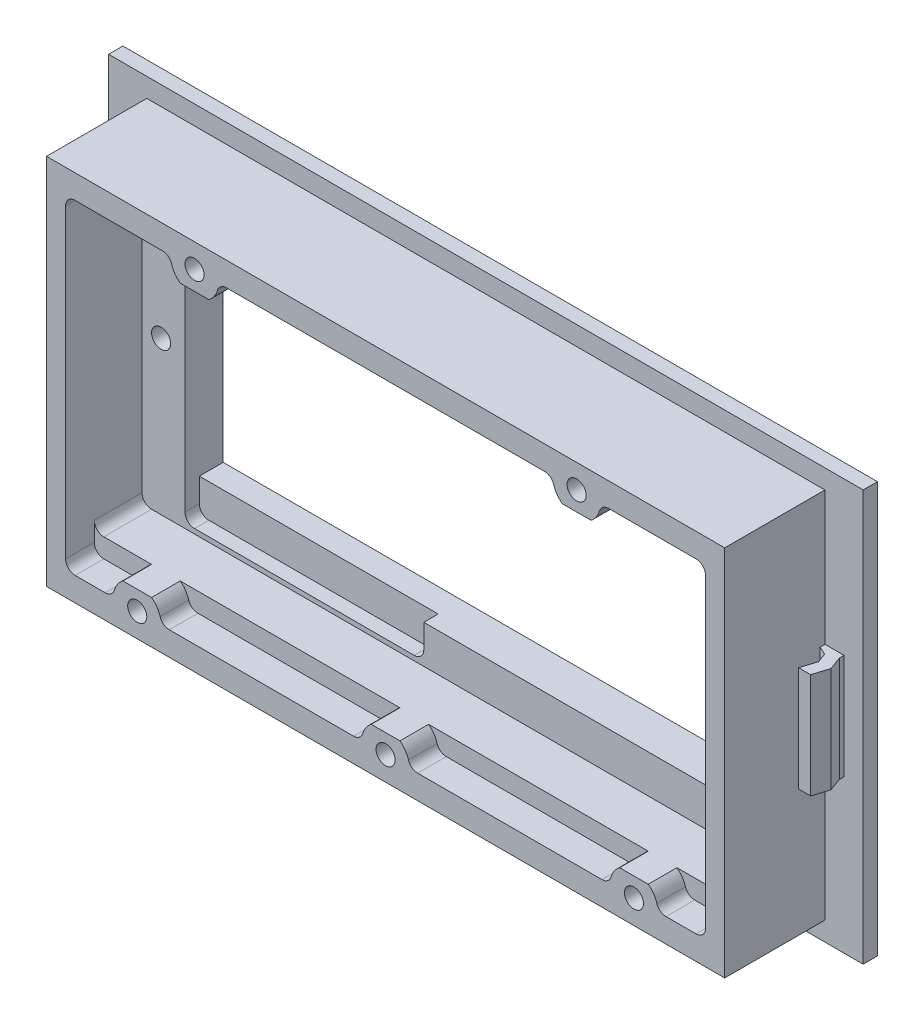
SolidWorks part; units mm, degrees
ref_plane "Спереди" through (0, 0, 0) normal (0, 0, 1) x (1, 0, 0)
ref_plane "Сверху" through (0, 0, 0) normal (0, 1, 0) x (1, 0, 0)
ref_plane "Справа" through (0, 0, 0) normal (1, 0, 0) x (0, 0, -1)
sketch "Эскиз1" plane through (0, 0, 0) normal (0, 0, 1) x (1, 0, 0)
  line L1 (39.5, 21.5) -> (-39.5, 21.5)
  line L2 (39.5, 21.5) -> (39.5, -21.5)
  line L3 (39.5, -21.5) -> (-39.5, -21.5)
  line L4 (-39.5, 21.5) -> (-39.5, -21.5)
  line L5 (39.5, 21.5) -> (-39.5, -21.5) construction
  line L6 (39.5, -21.5) -> (-39.5, 21.5) construction
  point P0 (0, 0)
  dimension "D1" = 43
  dimension "D2" = 79
extrude "Бобышка-Вытянуть1" add sketch "Эскиз1" along normal blind 1.5
sketch "Эскиз2" plane through (0, 0, 1.5) normal (0, 0, 1) x (1, 0, 0)
  line L1 (35.5, 19.5) -> (-35.5, 19.5)
  line L2 (35.5, 19.5) -> (35.5, -19.5)
  line L3 (35.5, -19.5) -> (-35.5, -19.5)
  line L4 (-35.5, 19.5) -> (-35.5, -19.5)
  line L5 (35.5, 19.5) -> (-35.5, -19.5) construction
  line L6 (35.5, -19.5) -> (-35.5, 19.5) construction
  point P0 (0, 0)
  dimension "D1" = 39
  dimension "D2" = 71
extrude "Бобышка-Вытянуть2" add sketch "Эскиз2" along normal blind 10.5
sketch "Эскиз3" plane through (0, 0, 12) normal (0, 0, 1) x (1, 0, 0)
  line L1 (-33.5, 15) -> (33.5, 15)
  line L2 (-33.5, 15) -> (-33.5, -15)
  line L3 (-33.5, -15) -> (33.5, -15)
  line L4 (33.5, 15) -> (33.5, -15)
  line L5 (-33.5, 15) -> (33.5, -15) construction
  line L6 (-33.5, -15) -> (33.5, 15) construction
  point P0 (0, 0)
  dimension "D1" = 67
  dimension "D2" = 30
extrude "Вырез-Вытянуть1" cut sketch "Эскиз3" against normal blind 8 contours L2 L3 L4 L1
sketch "Эскиз4" plane through (0, 0, 4) normal (0, 0, 1) x (1, 0, 0)
  line L0 (0, 15) -> (0, 0.5) construction
  line L5 (-33.5, 15) -> (33.5, 15) construction
  line L7 (-29, 12) -> (29, 12)
  line L8 (-29, 12) -> (-29, -11)
  line L9 (-29, -11) -> (29, -11)
  line L10 (29, 12) -> (29, -11)
  line L11 (-29, 12) -> (29, -11) construction
  line L12 (-29, -11) -> (29, 12) construction
  point P10 (0, 0)
  dimension "D1" = 58
  dimension "D2" = 23
  dimension "D3" = 3
extrude "Вырез-Вытянуть2" cut sketch "Эскиз4" against normal through all
sketch "Эскиз5" plane through (0, -19.5, 0) normal (0, -1, 0) x (1, 0, 0)
  line L0 (-27.6084, 3.216) -> (3.3873, 3.216) construction
  text T0 "BOTTOM HERE"
sketch "Эскиз6" plane through (0, 0, 12) normal (0, 0, 1) x (1, 0, 0)
  line L0 (-35.5, -19.5) -> (35.5, -19.5) construction
  line L3 (-35.5, 19.5) -> (-35.5, -19.5) construction
  line L5 (0, 0) -> (0, -17) construction
  line L6 (0, 0) -> (0, 17) construction
  line L7 (0, 17) -> (20, 17) construction
  line L8 (0, 17) -> (-20, 17) construction
  circle A0 centre (-26, -17) radius 1
  circle A1 centre (0, -17) radius 1
  circle A2 centre (26, -17) radius 1
  circle A3 centre (20, 17) radius 1
  circle A4 centre (-20, 17) radius 1
  dimension "D3" = 2
  dimension "D8" = 2
  dimension "D10" = 2
  dimension "D1" = 2.5
  dimension "D2" = 9.5
  dimension "D5" = 52
  dimension "D6" = 2.5
  dimension "D7" = 34
  dimension "D9" = 20
  dimension "D11" = 20
  dimension "D4" = 3
extrude "Вырез-Вытянуть3" cut sketch "Эскиз6" against normal blind 9 draft 4
sketch "Эскиз7" plane through (0, 0, 4) normal (0, 0, 1) x (1, 0, 0)
  line L0 (-33.5, 15) -> (-33.5, -15) construction
  line L2 (-33.5, -15) -> (33.5, -15) construction
  circle A0 centre (-31.5, 1) radius 1
  point P6 (-30.0765, -15)
  dimension "D3" = 2
  dimension "D1" = 2
  dimension "D2" = 16
extrude "Вырез-Вытянуть4" cut sketch "Эскиз7" against normal blind 3 draft 4
mirror "Зеркальное отражение1" about plane through (0, 0, 0) normal (1, 0, 0) of "Вырез-Вытянуть4"
sketch "Эскиз8" plane through (0, 0, 12) normal (0, 0, 1) x (1, 0, 0)
  line L2 (-17.5, 17) -> (17.5, 17)
  line L3 (33.5, 15) -> (33.5, 17)
  line L4 (33.5, 17) -> (22.5, 17)
  line L5 (33.5, -15) -> (33.5, -17)
  line L6 (33.5, -17) -> (28.5, -17)
  line L7 (33.5, 15) -> (33.5, -15)
  line L8 (23.5, -17) -> (2.5, -17)
  line L9 (-2.5, -17) -> (-23.5, -17)
  line L10 (-33.5, 15) -> (-33.5, 17)
  line L11 (-33.5, 17) -> (-22.5, 17)
  line L12 (-33.5, -15) -> (-33.5, -17)
  line L13 (-33.5, -17) -> (-28.5, -17)
  line L14 (-33.5, 15) -> (-33.5, -15)
  arc A0 (-22.5, 17) -> (-17.5, 17) centre (-20, 17) ccw
  arc A1 (17.5, 17) -> (22.5, 17) centre (20, 17) ccw
  arc A2 (28.5, -17) -> (23.5, -17) centre (26, -17) ccw
  arc A3 (-23.5, -17) -> (-28.5, -17) centre (-26, -17) ccw
  arc A4 (2.5, -17) -> (-2.5, -17) centre (0, -17) ccw
  dimension "D1" = 2.5
  dimension "D2" = 2.5
  dimension "D3" = 2.5
  dimension "D4" = 2.5
  dimension "D5" = 2.5
extrude "Вырез-Вытянуть5" cut sketch "Эскиз8" against normal blind 3
fillet "Скругление1" radius 1 18 edges at (-33.5, 15, 6.5) (33.5, 15, 6.5) (33.5, -15, 6.5) (-33.5, -15, 6.5) (-33.5, -17, 10.5) (33.5, -17, 10.5) (33.5, 17, 10.5) (-33.5, 17, 10.5) (-22.5, 17, 10.5) (-17.5, 17, 10.5) (-28.5, -17, 10.5) (-23.5, -17, 10.5) (-2.5, -17, 10.5) (2.5, -17, 10.5) (23.5, -17, 10.5) (17.5, 17, 10.5) (28.5, -17, 10.5) (22.5, 17, 10.5)
sketch "Эскиз9" plane through (0, 0, 4) normal (0, 0, 1) x (1, 0, 0)
  line L0 (-32.5, -15) -> (32.5, -15) construction
  line L1 (-29, -11) -> (-4, -11)
  line L2 (-29, -11) -> (-29, -14.5)
  line L3 (-29, -14.5) -> (-4, -14.5)
  line L4 (-4, -11) -> (-4, -14.5)
  dimension "D1" = 25
  dimension "D2" = 0.5
extrude "Вырез-Вытянуть6" cut sketch "Эскиз9" against normal blind 1.5
fillet "Скругление2" radius 1 2 edges at (-4, -14.5, 3.25) (-29, -14.5, 3.25)
sketch "Эскиз14" plane through (0, 0, 0) normal (0, 1, 0) x (1, 0, 0)
  line L0 (-35.5, -1.5) -> (-37.5, -1.5)
  line L1 (39.5, -1.5) -> (-39.5, -1.5) construction
  line L2 (-37.5, -1.5) -> (-37.5, -2)
  line L3 (-37.5, -2) -> (-38, -3.3737)
  line L4 (-37.5, -2) -> (-37.5, -3.6265) construction
  line L5 (-35.5, -1.5) -> (-35.5, -2)
  line L6 (-35.5, -12) -> (-35.5, -1.5) construction
  line L7 (-38, -3.3737) -> (-37.5, -5)
  line L8 (-37.5, -5) -> (-37.5, -3.6265) construction
  line L9 (-36.3724, -2.4104) -> (-36.7347, -3.4059)
  line L10 (-36.7347, -3.4059) -> (-36.2455, -4.997)
  line L11 (-36.7347, -3.4059) -> (-36.353, -4.6473) construction
  line L12 (-37.5, -5) -> (-36.2455, -4.997)
  line L13 (-35.5, -2) -> (-36.3724, -2.4104)
  dimension "D1" = 2
  dimension "D2" = 0.5
  dimension "D3" = 20
  dimension "D4" = 0.5
  dimension "D5" = 0.5
  dimension "D6" = 1.8737
  dimension "D7" = 3.5
  dimension "D8" = 1.2
extrude "Бобышка-Вытянуть3" add sketch "Эскиз14" along normal blind 5.5 and the other way blind 5.5
mirror "Зеркальное отражение2" about plane through (0, 0, 0) normal (1, 0, 0) of "Бобышка-Вытянуть3"
